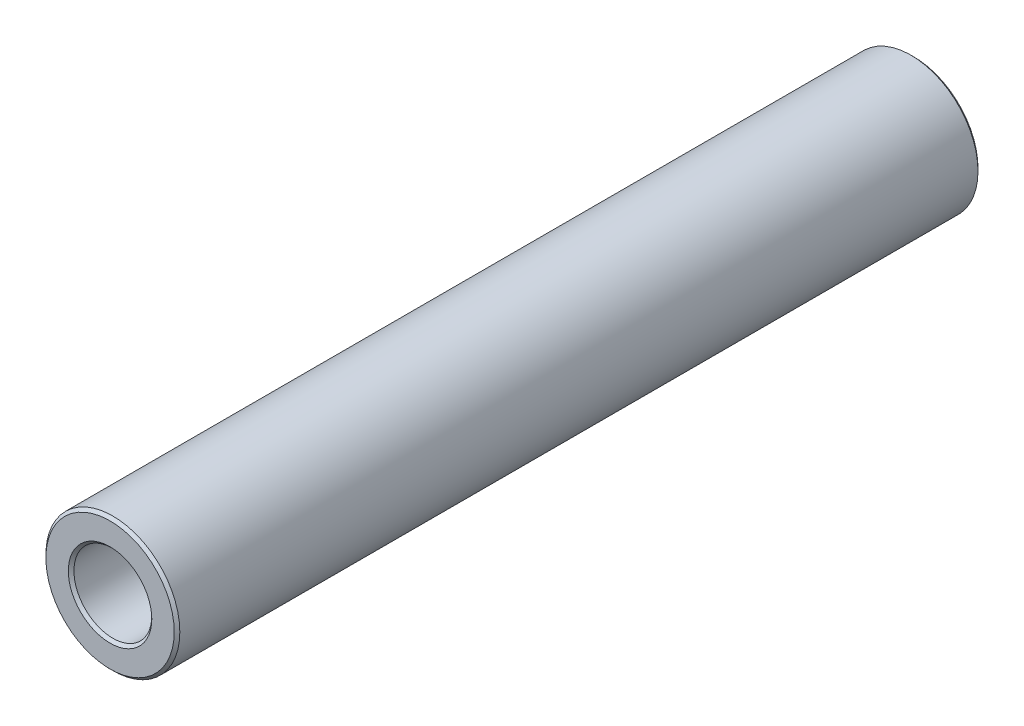
SolidWorks part; units mm, degrees
ref_plane "Front Plane" through (0, 0, 0) normal (0, 0, 1) x (1, 0, 0)
ref_plane "Top Plane" through (0, 0, 0) normal (0, 1, 0) x (1, 0, 0)
ref_plane "Right Plane" through (0, 0, 0) normal (1, 0, 0) x (0, 0, -1)
sketch "Sketch1" plane through (0, 0, 0) normal (0, 0, 1) x (1, 0, 0)
  circle A0 centre (0, 0) radius 4.7625 construction
  circle A1 centre (0, 0) radius 2.7686 construction
  point P4 (0, 4.7625)
  dimension "ID" = 5.5372
  dimension "OD" = 9.525
sketch "Sketch2" plane through (0, 0, 0) normal (1, 0, 0) x (0, 0, -1)
  line L0 (-28.575, 4.7625) -> (28.575, 4.7625) construction
  dimension "Length" = 57.15
sketch "Sketch3" plane through (0, 0, 0) normal (0, 0, 1) x (1, 0, 0)
  circle A0 centre (0, 0) radius 2.7686 construction
  circle A1 centre (0, 0) radius 4.7625 construction
  circle A2 centre (0, 0) radius 2.7686
  circle A3 centre (0, 0) radius 4.7625
extrude "Boss-Extrude1" add sketch "Sketch3" against normal up to vertex (28.575 mm away) and the other way up to vertex (28.575 mm away) up to point (0, 4.7625, -28.575) other way up to point (0, 4.7625, 28.575)
chamfer "Chamfer1" distance 0.1994 angle 45 1 edges at (4.7625, 0, 28.575)
equation "\"D1@Chamfer1\"=(\"OD@Sketch1\"-\"ID@Sketch1\")*0.05"
